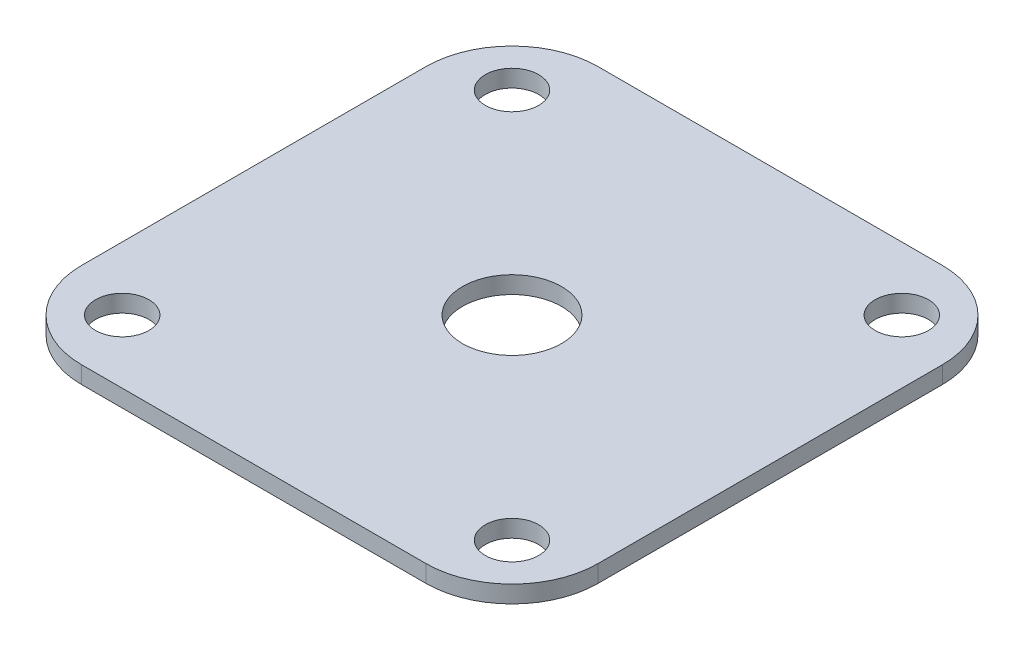
SolidWorks part; units mm, degrees
ref_plane "Front Plane" through (0, 0, 0) normal (0, 0, 1) x (1, 0, 0)
ref_plane "Top Plane" through (0, 0, 0) normal (0, 1, 0) x (1, 0, 0)
ref_plane "Right Plane" through (0, 0, 0) normal (1, 0, 0) x (0, 0, -1)
sketch "Sketch1" plane through (0, 0, 0) normal (0, 1, 0) x (1, 0, 0)
  line L0 (-58.3846, 0) -> (58.3846, 0) construction
  line L1 (0, -45.6346) -> (0, 45.6346) construction
  line L3 (-20, -30) -> (20, -30)
  line L4 (-30, -20) -> (-30, 20)
  line L5 (-20, 30) -> (20, 30)
  line L6 (30, -20) -> (30, 20)
  line L7 (-30, -30) -> (30, 30) construction
  line L8 (-30, 30) -> (30, -30) construction
  arc A0 (20, -30) -> (30, -20) centre (20, -20) ccw
  arc A1 (20, 30) -> (30, 20) centre (20, 20) cw
  arc A2 (-20, -30) -> (-30, -20) centre (-20, -20) cw
  arc A3 (-30, 20) -> (-20, 30) centre (-20, 20) cw
  circle A4 centre (-22.6442, 22.6442) radius 3.1
  circle A5 centre (-22.6442, -22.6442) radius 3.1
  circle A6 centre (22.6442, -22.6442) radius 3.1
  circle A7 centre (22.6442, 22.6442) radius 3.1
  point P0 (0, 0)
  point P4 (0, 0)
  point P7 (0, 0)
  dimension "D3" = 10
  dimension "D4" = 6.2
  dimension "D1" = 60
  dimension "D2" = 60
  dimension "D5" = 45.2885
extrude "Boss-Extrude1" add sketch "Sketch1" along normal blind 2
sketch "Sketch2" plane through (0, 2, 0) normal (0, 1, 0) x (1, 0, 0)
  circle A0 centre (0, 0) radius 5.75
  dimension "D1" = 11.5
extrude "Cut-Extrude1" cut sketch "Sketch2" against normal through all
